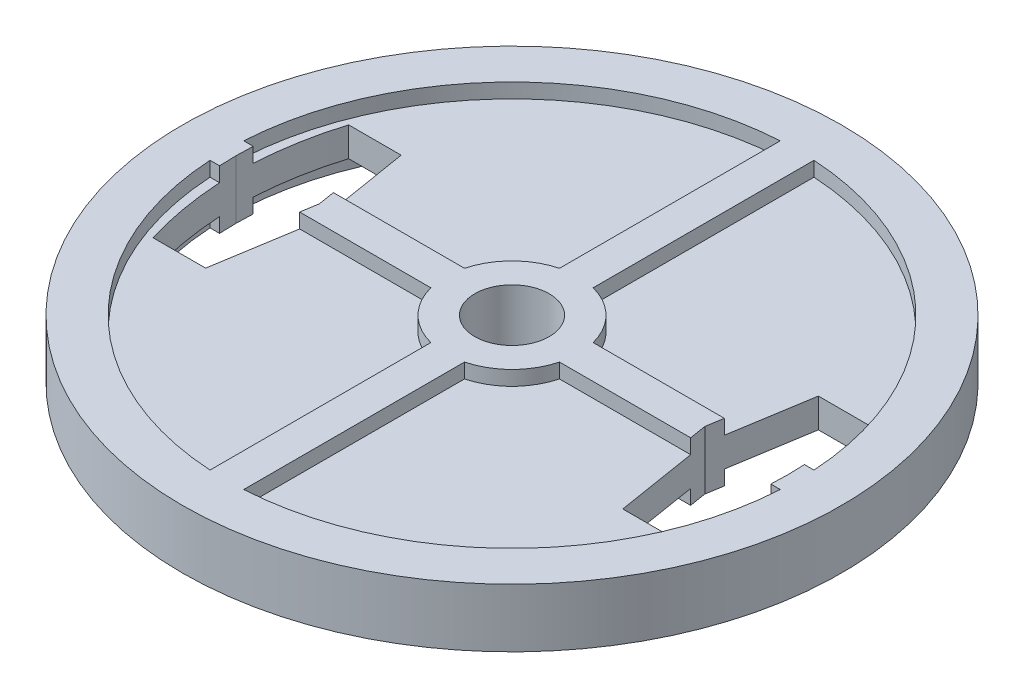
SolidWorks part; units mm, degrees
material "Gray Cast Iron"
ref_plane "Front Plane" through (0, 0, 0) normal (0, 0, 1) x (1, 0, 0)
ref_plane "Top Plane" through (0, 0, 0) normal (0, 1, 0) x (1, 0, 0)
ref_plane "Right Plane" through (0, 0, 0) normal (1, 0, 0) x (0, 0, -1)
sketch "Sketch1" plane through (0, 0, 0) normal (0, 1, 0) x (1, 0, 0)
  circle A0 centre (0, 0) radius 225
  circle A1 centre (0, 0) radius 25.4
  dimension "D1" = 450
  dimension "D2" = 50.8
extrude "Boss-Extrude1" add sketch "Sketch1" along normal blind 20
sketch "Sketch2" plane through (0, 0, 0) normal (0, 1, 0) x (1, 0, 0)
  line L0 (-178.2585, 66.7648) -> (-142.4202, 66.7648)
  line L1 (-142.4202, 66.7648) -> (-131.6119, 0)
  line L2 (-188.4981, 27.8391) -> (-188.4981, -27.8391) construction
  line L3 (-22, 0) -> (22, 0) construction
  line L4 (-142.4202, -66.7648) -> (-131.6119, 0)
  line L5 (-178.2585, -66.7648) -> (-142.4202, -66.7648)
  line L6 (0, -22) -> (0, 22) construction
  line L7 (178.2585, -66.7648) -> (142.4202, -66.7648)
  line L8 (142.4202, -66.7648) -> (131.6119, 0)
  line L9 (142.4202, 66.7648) -> (131.6119, 0)
  line L10 (178.2585, 66.7648) -> (142.4202, 66.7648)
  spline S0 degree 3 poles (-188.4981, 0) (-188.4981, 23.1992) (-184.2043, 48.2032) (-178.2585, 66.7648) knots 0 0 0 0 1 1 1 1
  spline S1 degree 3 poles (-188.4981, 0) (-188.4981, -23.1992) (-184.2043, -48.2032) (-178.2585, -66.7648) knots 0 0 0 0 1 1 1 1
  spline S2 degree 3 poles (188.4981, 0) (188.4981, -23.1992) (184.2043, -48.2032) (178.2585, -66.7648) knots 0 0 0 0 1 1 1 1
  spline S3 degree 3 poles (188.4981, 0) (188.4981, 23.1992) (184.2043, 48.2032) (178.2585, 66.7648) knots 0 0 0 0 1 1 1 1
extrude "Cut-Extrude1" cut sketch "Sketch2" against normal through all and the other way through all
sketch "Sketch3" plane through (0, 0, 0) normal (0, 1, 0) x (1, 0, 0)
  line L0 (-11.5, 43.9194) -> (-11.5, 194.6606)
  line L1 (0, -11) -> (0, 11) construction
  line L2 (11.5, 43.9194) -> (11.5, 194.6606)
  line L3 (43.9194, 11.5) -> (194.6606, 11.5)
  line L4 (43.9194, -11.5) -> (194.6606, -11.5)
  line L5 (11.5, -43.9194) -> (11.5, -194.6606)
  line L6 (-11.5, -43.9194) -> (-11.5, -194.6606)
  line L7 (-43.9194, -11.5) -> (-194.6606, -11.5)
  line L8 (-43.9194, 11.5) -> (-194.6606, 11.5)
  line L9 (0, 0) -> (11.5, 43.9194) construction
  arc A0 (-11.5, 194.6606) -> (-194.6606, 11.5) centre (0, 0) ccw
  arc A1 (11.5, -43.9194) -> (43.9194, -11.5) centre (0, 0) ccw
  circle A2 centre (0, 0) radius 25.4 construction
  arc A3 (-194.6606, -11.5) -> (-11.5, -194.6606) centre (0, 0) ccw
  arc A4 (-43.9194, -11.5) -> (-11.5, -43.9194) centre (0, 0) ccw
  arc A5 (43.9194, 11.5) -> (11.5, 43.9194) centre (0, 0) ccw
  arc A6 (11.5, -194.6606) -> (194.6606, -11.5) centre (0, 0) ccw
  arc A7 (194.6606, 11.5) -> (11.5, 194.6606) centre (0, 0) ccw
  arc A8 (-11.5, 43.9194) -> (-43.9194, 11.5) centre (0, 0) ccw
  dimension "D1" = 390
  dimension "D2" = 20
  dimension "D3" = 23
  dimension "D4" = 4
extrude "Cut-Extrude2" cut sketch "Sketch3" against normal blind 10 from surface at 20 starting at face at (-160.2446, 20, -11.1275)
mirror "Mirror2" about plane through (0, 0, 0) normal (0, 1, 0) of bodies 103
